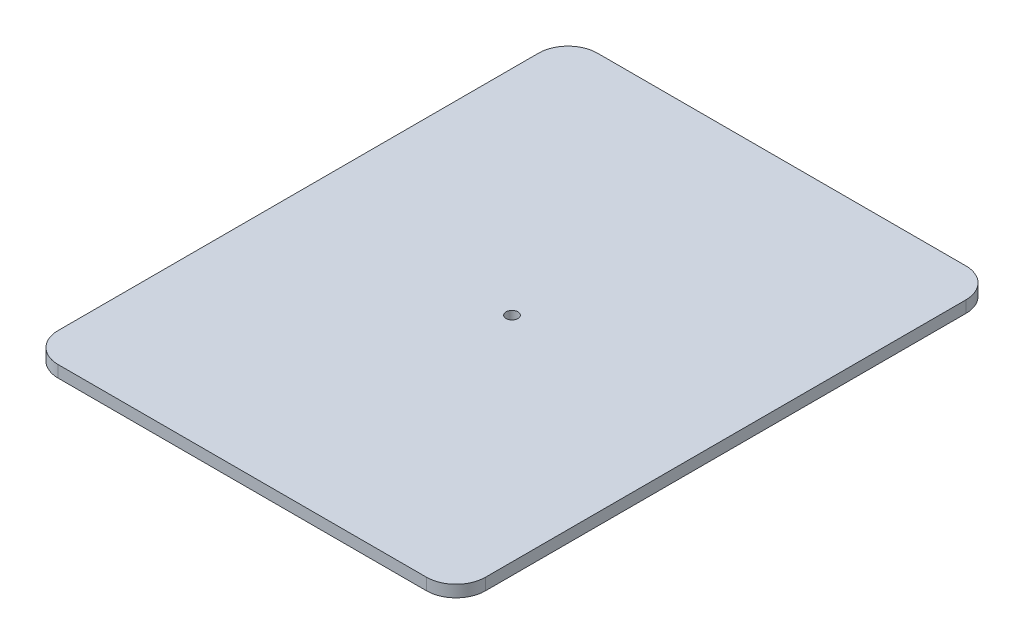
SolidWorks part; units mm, degrees
ref_plane "Front Plane" through (0, 0, 0) normal (0, 0, 1) x (1, 0, 0)
ref_plane "Top Plane" through (0, 0, 0) normal (0, 1, 0) x (1, 0, 0)
ref_plane "Right Plane" through (0, 0, 0) normal (1, 0, 0) x (0, 0, -1)
sketch "Sketch1" plane through (0, 0, 0) normal (0, 1, 0) x (1, 0, 0)
  line L1 (100, 100) -> (-100, 100)
  line L2 (100, 100) -> (100, -100)
  line L3 (100, -100) -> (-100, -100)
  line L4 (-100, 100) -> (-100, -100)
  line L5 (100, 100) -> (-100, -100) construction
  line L6 (100, -100) -> (-100, 100) construction
  circle A31 centre (0, 0) radius 2
  point P0 (0, 0)
  dimension "D1" = 200
extrude "Boss-Extrude1" add sketch "Sketch1" along normal blind 4
fillet "Fillet1" radius 10 4 edges at (100, 2, -100) (100, 2, 100) (-100, 2, 100) (-100, 2, -100)
sketch "Sketch2" plane through (0, 4, 0) normal (0, 1, 0) x (1, 0, 0)
  line L1 (-62.5, 91.5) -> (62.5, 91.5)
  line L2 (-72.5, 81.5) -> (-72.5, -81.5)
  line L3 (-62.5, -91.5) -> (62.5, -91.5)
  line L4 (72.5, 81.5) -> (72.5, -81.5)
  line L5 (-72.5, 91.5) -> (72.5, -91.5) construction
  line L6 (-72.5, -91.5) -> (72.5, 91.5) construction
  line L7 (-164.4017, 181.6232) -> (167.9646, 181.6232)
  line L8 (-164.4017, 181.6232) -> (-164.4017, -177.1266)
  line L9 (-164.4017, -177.1266) -> (167.9646, -177.1266)
  line L10 (167.9646, 181.6232) -> (167.9646, -177.1266)
  line L11 (-164.4017, 181.6232) -> (167.9646, -177.1266) construction
  line L12 (-164.4017, -177.1266) -> (167.9646, 181.6232) construction
  arc A0 (-72.5, -81.5) -> (-62.5, -91.5) centre (-62.5, -81.5) ccw
  arc A1 (62.5, -91.5) -> (72.5, -81.5) centre (62.5, -81.5) ccw
  arc A2 (62.5, 91.5) -> (72.5, 81.5) centre (62.5, 81.5) cw
  arc A3 (-62.5, 91.5) -> (-72.5, 81.5) centre (-62.5, 81.5) ccw
  point P0 (0, 0)
  point P18 (1.7814, 2.2483)
  dimension "D3" = 10
  dimension "D1" = 183
  dimension "D2" = 145
extrude "Cut-Extrude1" cut sketch "Sketch2" against normal blind 10
